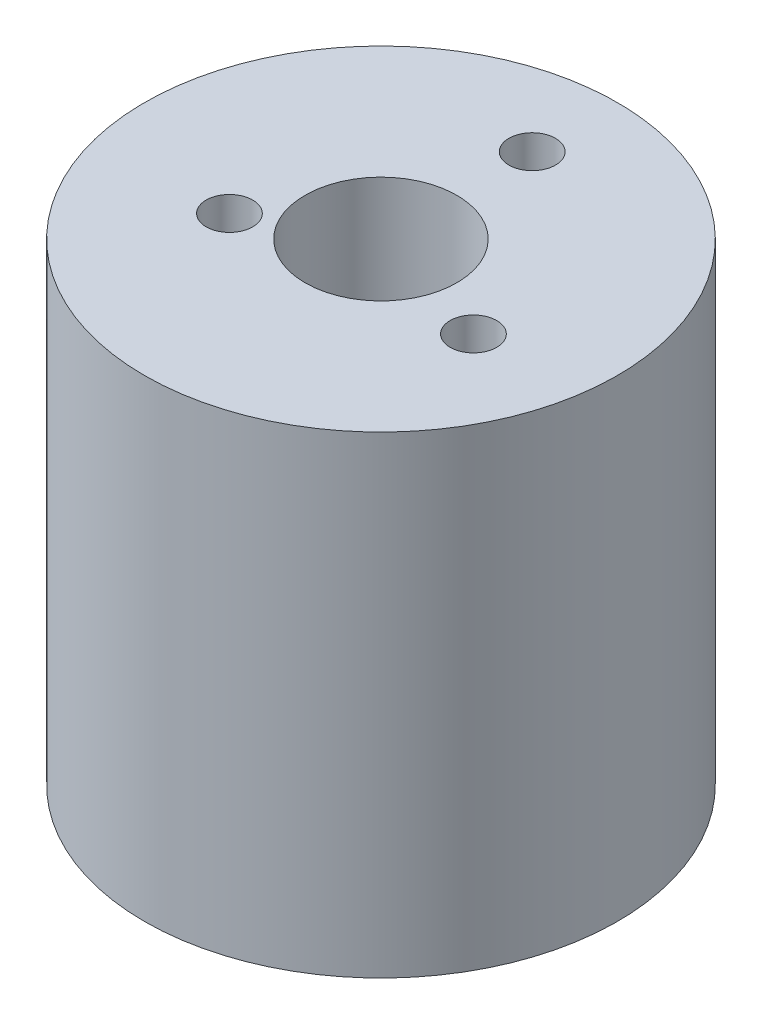
SolidWorks part; units mm, degrees
ref_plane "Front Plane" through (0, 0, 0) normal (0, 0, 1) x (1, 0, 0)
ref_plane "Top Plane" through (0, 0, 0) normal (0, 1, 0) x (1, 0, 0)
ref_plane "Right Plane" through (0, 0, 0) normal (1, 0, 0) x (0, 0, -1)
sketch "Sketch1" plane through (0, 0, 0) normal (0, 1, 0) x (1, 0, 0)
  circle A0 centre (0, 0) radius 12.7
  dimension "D1" = 25.4
extrude "Boss-Extrude1" add sketch "Sketch1" along normal blind 25.4
sketch "Sketch2" plane through (0, 25.4, 0) normal (0, 1, 0) x (1, 0, 0)
  circle A0 centre (0, 0) radius 4.075
  dimension "D1" = 8.15
extrude "Cut-Extrude1" cut sketch "Sketch2" against normal blind 19.05
sketch "Sketch3" plane through (0, 25.4, 0) normal (0, 1, 0) x (1, 0, 0)
  circle A1 centre (6.8999, -1.9309) radius 1.25
  circle A2 centre (-5.2588, -2.8785) radius 1.25
  circle A3 centre (0, 8.125) radius 1.25
  circle A4 centre (0, 0) radius 4.075 construction
  circle A5 centre (0, 0) radius 4.075 construction
  point P0 (0, 8.125)
  point P5 (-0.9408, 8.5985)
  point P12 (0.5471, 1.1052)
  dimension "D2" = 1.84
  dimension "D3" = 2.5
  dimension "D4" = 0.67
  dimension "D5" = 2.8
  dimension "D1" = 3
extrude "Cut-Extrude2" cut sketch "Sketch3" against normal blind 12 contours A3 | A2 | A1
